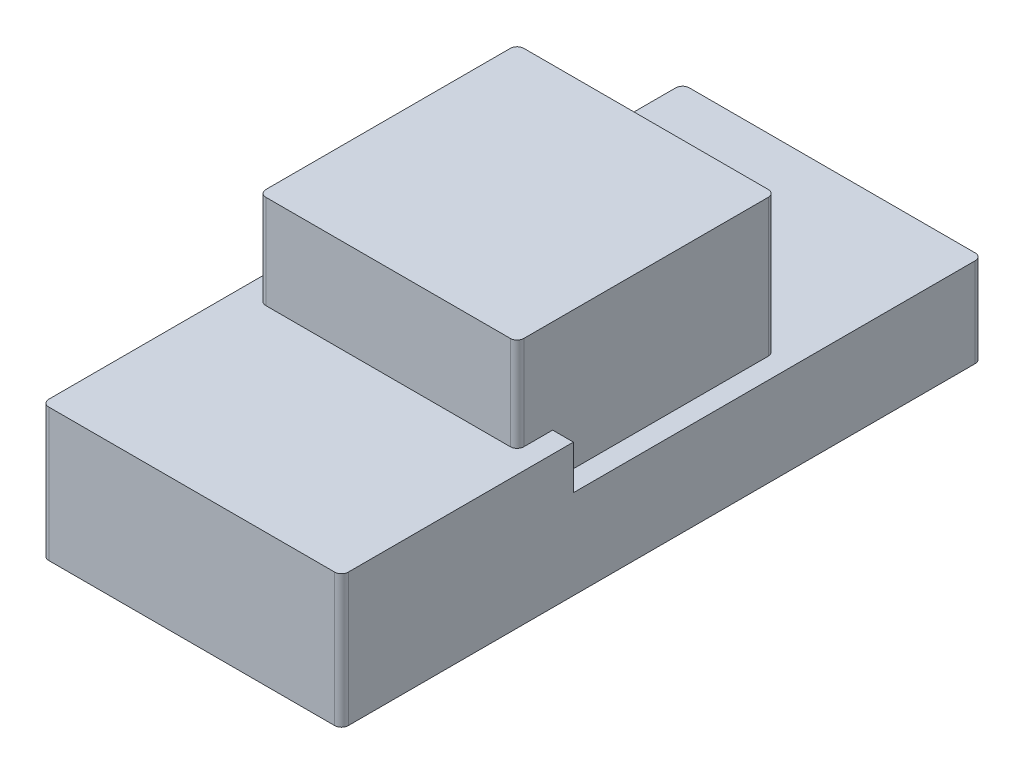
SolidWorks part; units mm, degrees
ref_plane "Front Plane" through (0, 0, 0) normal (0, 0, 1) x (1, 0, 0)
ref_plane "Top Plane" through (0, 0, 0) normal (0, 1, 0) x (1, 0, 0)
ref_plane "Right Plane" through (0, 0, 0) normal (1, 0, 0) x (0, 0, -1)
sketch "Sketch1" plane through (0, 0, 0) normal (0, 1, 0) x (1, 0, 0)
  line L1 (22.115, -47.3) -> (-22.115, -47.3)
  line L2 (22.115, -47.3) -> (22.115, 47.3)
  line L3 (22.115, 47.3) -> (-22.115, 47.3)
  line L4 (-22.115, -47.3) -> (-22.115, 47.3)
  line L5 (22.115, -47.3) -> (-22.115, 47.3) construction
  line L6 (22.115, 47.3) -> (-22.115, -47.3) construction
  point P0 (0, 0)
  dimension "D1" = 94.6
  dimension "D2" = 44.23
extrude "Boss-Extrude1" add sketch "Sketch1" along normal blind 13.17
sketch "Sketch2" plane through (0, 13.17, 0) normal (0, 1, 0) x (1, 0, 0)
  line L0 (-22.115, -47.3) -> (22.115, -47.3) construction
  line L1 (19.05, -18.3) -> (-19.05, -18.3)
  line L2 (19.05, -18.3) -> (19.05, 19.8)
  line L3 (19.05, 19.8) -> (-19.05, 19.8)
  line L4 (-19.05, -18.3) -> (-19.05, 19.8)
  line L5 (19.05, -18.3) -> (-19.05, 19.8) construction
  line L6 (19.05, 19.8) -> (-19.05, -18.3) construction
  point P0 (0, 0.75)
  dimension "D1" = 38.1
  dimension "D2" = 38.1
  dimension "D3" = 29
extrude "Boss-Extrude2" add sketch "Sketch2" along normal blind 20.33
fillet "Fillet1" radius 1 8 edges at (-22.115, 6.585, 47.3) (22.115, 6.585, 47.3) (19.05, 23.335, 18.3) (-19.05, 23.335, 18.3) (19.05, 23.335, -19.8) (-19.05, 23.335, -19.8) (22.115, 6.585, -47.3) (-22.115, 6.585, -47.3)
sketch "Sketch3" plane through (0, 13.17, 0) normal (0, 1, 0) x (1, 0, 0)
  line L0 (-22.115, -13.0435) -> (-19.05, -13.0435)
  line L1 (-22.115, 46.3) -> (-22.115, -46.3) construction
  line L2 (-19.05, 18.8) -> (-19.05, -17.3) construction
  line L3 (-19.05, -13.0435) -> (-19.05, -17.3)
  line L4 (1.2148, -18.3) -> (-18.05, -18.3)
  line L5 (-18.05, -18.3) -> (18.05, -18.3) construction
  line L6 (1.2148, -18.3) -> (18.05, -18.3)
  line L7 (19.05, -17.3) -> (19.05, -13.0435)
  line L8 (22.115, -46.3) -> (22.115, 46.3) construction
  line L9 (22.115, -17.3) -> (22.115, -46.3)
  line L10 (21.115, -47.3) -> (-21.115, -47.3)
  line L11 (-21.115, -47.3) -> (21.115, -47.3)
  line L12 (-22.115, -46.3) -> (-22.115, -13.0435)
  line L13 (-21.115, -47.3) -> (21.115, -47.3)
  line L14 (19.05, -17.3) -> (19.05, 18.8) construction
  line L15 (19.05, -13.0435) -> (22.115, -13.0435)
  line L16 (22.115, -13.0435) -> (22.115, -17.3)
  arc A0 (-19.05, -17.3) -> (-18.7571, -18.0071) centre (-18.05, -17.3) ccw
  arc A1 (-19.05, -17.3) -> (-18.05, -18.3) centre (-18.05, -17.3) ccw construction
  arc A2 (-18.7571, -18.0071) -> (-18.05, -18.3) centre (-18.05, -17.3) ccw
  arc A3 (18.05, -18.3) -> (18.7571, -18.0071) centre (18.05, -17.3) ccw
  arc A4 (18.05, -18.3) -> (19.05, -17.3) centre (18.05, -17.3) ccw construction
  arc A5 (18.7571, -18.0071) -> (19.05, -17.3) centre (18.05, -17.3) ccw
  arc A6 (18.05, -18.3) -> (19.05, -17.3) centre (18.05, -17.3) ccw construction
  arc A7 (22.115, -46.3) -> (21.8221, -47.0071) centre (21.115, -46.3) cw
  arc A8 (21.115, -47.3) -> (22.115, -46.3) centre (21.115, -46.3) ccw construction
  arc A9 (21.8221, -47.0071) -> (21.115, -47.3) centre (21.115, -46.3) cw
  arc A10 (-21.115, -47.3) -> (-21.8221, -47.0071) centre (-21.115, -46.3) cw
  arc A11 (-22.115, -46.3) -> (-21.115, -47.3) centre (-21.115, -46.3) ccw construction
  arc A12 (-21.8221, -47.0071) -> (-22.115, -46.3) centre (-21.115, -46.3) cw
  line M1 (-19.05, -17.3) -> (-19.05, 18.8)
  line M5 (19.05, 18.8) -> (19.05, -17.3)
  arc M6 (19.05, -17.3) -> (18.05, -18.3) centre (18.05, -17.3) cw
  line M7 (18.05, -18.3) -> (-18.05, -18.3)
  arc M8 (-18.05, -18.3) -> (-19.05, -17.3) centre (-18.05, -17.3) cw
  line M9 (-22.115, 46.3) -> (-22.115, -46.3)
  arc M10 (-22.115, -46.3) -> (-21.115, -47.3) centre (-21.115, -46.3) ccw
  line M11 (-21.115, -47.3) -> (21.115, -47.3)
  arc M12 (21.115, -47.3) -> (22.115, -46.3) centre (21.115, -46.3) ccw
  line M13 (22.115, -46.3) -> (22.115, 46.3)
extrude "Boss-Extrude3" add sketch "Sketch3" along normal blind 6.47 contours L15 L0 M5 M6 M7 M8 M1 M9 M10 M11 M12 M13
